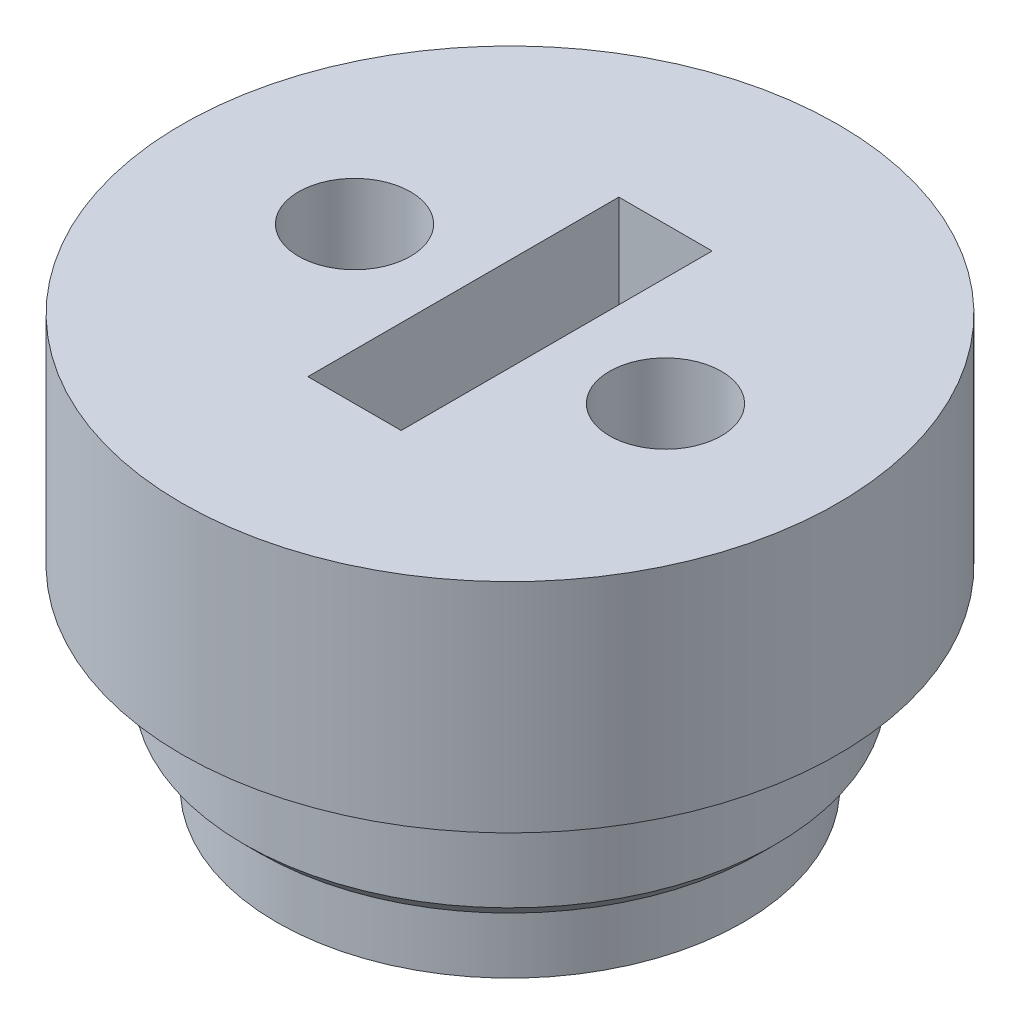
SolidWorks part; units mm, degrees
material "ABS"
ref_plane "Ebene vorne" through (0, 0, 0) normal (0, 0, 1) x (1, 0, 0)
ref_plane "Ebene oben" through (0, 0, 0) normal (0, 1, 0) x (1, 0, 0)
ref_plane "Ebene rechts" through (0, 0, 0) normal (1, 0, 0) x (0, 0, -1)
sketch "Skizze1" plane through (0, 0, 0) normal (0, 1, 0) x (1, 0, 0)
  line L1 (-1.5, -5) -> (1.5, -5)
  line L2 (-1.5, -5) -> (-1.5, 5)
  line L3 (-1.5, 5) -> (1.5, 5)
  line L4 (1.5, -5) -> (1.5, 5)
  line L5 (-1.5, -5) -> (1.5, 5) construction
  line L6 (-1.5, 5) -> (1.5, -5) construction
  circle A0 centre (0, 0) radius 8.55
  dimension "D1" = 17.1
  dimension "D2" = 10
  dimension "D3" = 3
extrude "Aufsatz-Linear austragen1" add sketch "Skizze1" along normal blind 4
sketch "Skizze2" plane through (0, 4, 0) normal (0, 1, 0) x (1, 0, 0)
  line L0 (1.5, 5) -> (-1.5, 5) construction
  line L1 (-1.5, 5) -> (-1.5, -5) construction
  line L3 (1.5, -5) -> (1.5, 5) construction
  line L4 (-1.5, -5) -> (1.5, -5) construction
  line L5 (-1.5, -5) -> (1.5, -5)
  line L6 (1.5, -5) -> (1.5, 5)
  line L7 (-1.5, 5) -> (-1.5, -5)
  line L8 (1.5, 5) -> (-1.5, 5)
  circle A3 centre (0, 0) radius 10.55
  circle A4 centre (0, 0) radius 10.55
  dimension "D1" = 2
extrude "Aufsatz-Linear austragen2" add sketch "Skizze2" along normal blind 7
sketch "Skizze3" plane through (0, 0, 0) normal (0, -1, 0) x (1, 0, 0)
  line L0 (1.5, 5) -> (1.5, -5) construction
  line L1 (1.5, 5) -> (1.5, -5)
  line L2 (-1.5, 5) -> (1.5, 5) construction
  line L4 (-1.5, 5) -> (1.5, 5)
  line L5 (1.5, -5) -> (-1.5, -5) construction
  line L6 (1.5, -5) -> (-1.5, -5)
  line L7 (-1.5, -5) -> (-1.5, 5) construction
  line L8 (-1.5, -5) -> (-1.5, 5)
  circle A0 centre (0, 0) radius 7.5
  dimension "D1" = 15
extrude "Aufsatz-Linear austragen3" add sketch "Skizze3" along normal blind 2.2
fillet "Verrundung1" [suppressed] radius 0.2
chamfer "Fase1" distance 0.5 angle 45 1 edges at (0, 0, 8.55)
sketch "Skizze4" plane through (0, 11, 0) normal (0, -1, 0) x (1, 0, 0)
  line L0 (-5, 0) -> (0, 0) construction
  line L1 (0, 0) -> (5, 0) construction
  circle A0 centre (-5, 0) radius 1.8
  circle A1 centre (5, 0) radius 1.8
  dimension "D1" = 3.6
  dimension "D2" = 10
extrude "Schnitt-Linear austragen1" cut sketch "Skizze4" along normal blind 10
